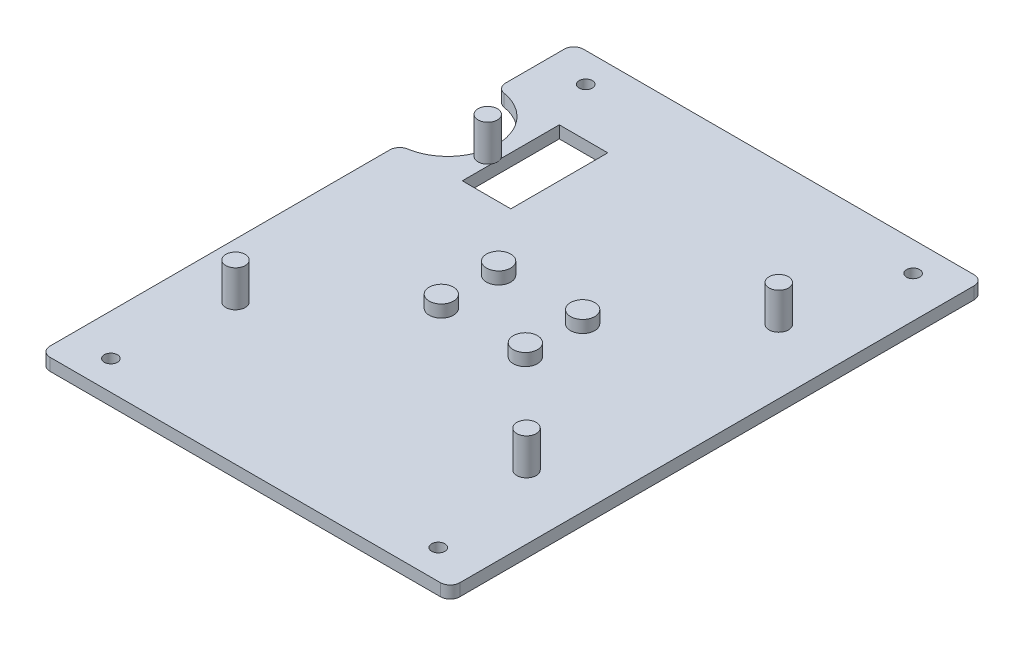
SolidWorks part; units mm, degrees
ref_plane "Front Plane" through (0, 0, 0) normal (0, 0, 1) x (1, 0, 0)
ref_plane "Top Plane" through (0, 0, 0) normal (0, 1, 0) x (1, 0, 0)
ref_plane "Right Plane" through (0, 0, 0) normal (1, 0, 0) x (0, 0, -1)
sketch "Sketch1" plane through (0, 0, 0) normal (0, 1, 0) x (1, 0, 0)
  line L0 (10.795, 132.0165) -> (96.52, 132.0165) construction
  line L1 (0, 139.7) -> (107.315, 139.7)
  line L2 (0, 139.7) -> (0, 0)
  line L3 (0, 0) -> (107.315, 0)
  line L4 (107.315, 139.7) -> (107.315, 0)
  line L5 (10.795, 7.6835) -> (96.52, 7.6835) construction
  line L6 (53.6575, 139.7) -> (53.6575, 132.0165) construction
  line L7 (0, 69.85) -> (107.315, 69.85) construction
  line L8 (53.6575, 7.6835) -> (53.6575, 0) construction
  circle A0 centre (10.795, 132.0165) radius 1.7272
  circle A1 centre (96.52, 132.0165) radius 1.7272
  circle A2 centre (96.52, 7.6835) radius 1.7272
  circle A3 centre (10.795, 7.6835) radius 1.7272
  dimension "D4" = 3.4544
  dimension "D1" = 107.315
  dimension "D2" = 139.7
  dimension "D3" = 85.725
  dimension "D5" = 7.6835
extrude "Boss-Extrude1" add sketch "Sketch1" along normal blind 3.2004
sketch "Sketch2" plane through (0, 3.2004, 0) normal (0, 1, 0) x (1, 0, 0)
  line L0 (0, 139.7) -> (0, 0) construction
  line L1 (107.315, 139.7) -> (0, 139.7) construction
  line L4 (22.86, 106.68) -> (0, 106.68) construction
  line L5 (29.21, 119.38) -> (16.51, 119.38)
  line L6 (29.21, 119.38) -> (29.21, 93.98)
  line L7 (29.21, 93.98) -> (16.51, 93.98)
  line L8 (16.51, 119.38) -> (16.51, 93.98)
  line L9 (22.86, 119.38) -> (22.86, 93.98) construction
  line L12 (0, 119.5054) -> (0, 93.8546)
  arc A0 (0, 119.5054) -> (0, 93.8546) centre (0, 106.68) cw
  dimension "D3" = 12.8254
  dimension "D2" = 33.02
  dimension "D4" = 22.86
  dimension "D5" = 12.7
  dimension "D6" = 25.4
extrude "Cut-Extrude1" cut sketch "Sketch2" against normal up to surface (3.2004 mm away) up to face at (53.6575, 0, -69.85)
sketch "Sketch3" plane through (0, 3.2004, 0) normal (0, 1, 0) x (1, 0, 0)
  line L8 (53.6575, 139.7) -> (53.6575, 0) construction
  line L12 (0, 0) -> (107.315, 0) construction
  line L13 (0, 139.7) -> (107.315, 139.7) construction
  line L74 (90.4875, 102.87) -> (90.4875, 36.83) construction
  line L76 (14.2875, 36.83) -> (14.2875, 102.87) construction
  line L78 (90.4875, 69.85) -> (14.2875, 69.85) construction
  circle A0 centre (90.4875, 102.87) radius 1.1303
  circle A1 centre (90.4875, 36.83) radius 1.1303
  circle A2 centre (14.2875, 36.83) radius 1.1303
  circle A3 centre (14.2875, 102.87) radius 1.1303
  point P18 (53.6575, 69.85)
  point P80 (52.3875, 69.85)
  dimension "D7" = 2.2606
  dimension "D1" = 1.27
  dimension "D5" = 76.2
  dimension "D6" = 66.04
extrude "Cut-Extrude2" cut sketch "Sketch3" against normal up to surface (3.2004 mm away) up to face at (22.86, 0, -106.68)
fillet "Fillet1" radius 2.54 6 edges at (0, 1.6002, -93.8546) (0, 1.6002, -119.5054) (107.315, 1.6002, -139.7) (107.315, 1.6002, 0) (0, 1.6002, 0) (0, 1.6002, -139.7)
sketch "Sketch4" plane through (0, 3.2004, 0) normal (0, 1, 0) x (1, 0, 0)
  line L0 (64.6575, 69.85) -> (42.6575, 69.85) construction
  line L2 (53.6575, 139.7) -> (53.6575, 0) construction
  line L3 (64.6575, 77.35) -> (64.6575, 62.35) construction
  line L4 (42.6575, 77.35) -> (42.6575, 62.35) construction
  circle A0 centre (64.6575, 77.35) radius 1.0249
  circle A1 centre (64.6575, 62.35) radius 1.0249
  circle A2 centre (42.6575, 77.35) radius 1.0249
  circle A3 centre (42.6575, 62.35) radius 1.0249
  dimension "D3" = 2.0498
  dimension "D1" = 22
  dimension "D2" = 15
extrude "Cut-Extrude3" cut sketch "Sketch4" against normal up to surface (3.2004 mm away) up to face at (14.2875, 0, -101.7397)
sketch "Sketch5" plane through (0, 3.2004, 0) normal (0, 1, 0) x (1, 0, 0)
  circle A0 centre (90.4875, 102.87) radius 2.54
  circle A1 centre (90.4875, 36.83) radius 2.54
  circle A2 centre (14.2875, 36.83) radius 2.54
  circle A3 centre (14.2875, 102.87) radius 2.54
  circle A4 centre (14.2875, 102.87) radius 1.1303 construction
  circle A5 centre (90.4875, 102.87) radius 1.1303 construction
  circle A6 centre (90.4875, 36.83) radius 1.1303 construction
  circle A7 centre (14.2875, 36.83) radius 1.1303 construction
  dimension "D1" = 5.08
extrude "Boss-Extrude2" add sketch "Sketch5" along normal blind 9.525
sketch "Sketch6" plane through (0, 3.2004, 0) normal (0, 1, 0) x (1, 0, 0)
  circle A0 centre (64.6575, 77.35) radius 3.175
  circle A1 centre (64.6575, 62.35) radius 3.175
  circle A2 centre (42.6575, 62.35) radius 3.175
  circle A3 centre (42.6575, 77.35) radius 3.175
  circle A4 centre (64.6575, 77.35) radius 1.0249 construction
  circle A5 centre (64.6575, 62.35) radius 1.0249 construction
  circle A6 centre (42.6575, 77.35) radius 1.0249 construction
  circle A7 centre (42.6575, 62.35) radius 1.0249 construction
  dimension "D1" = 6.35
extrude "Boss-Extrude3" add sketch "Sketch6" along normal blind 3.2004
